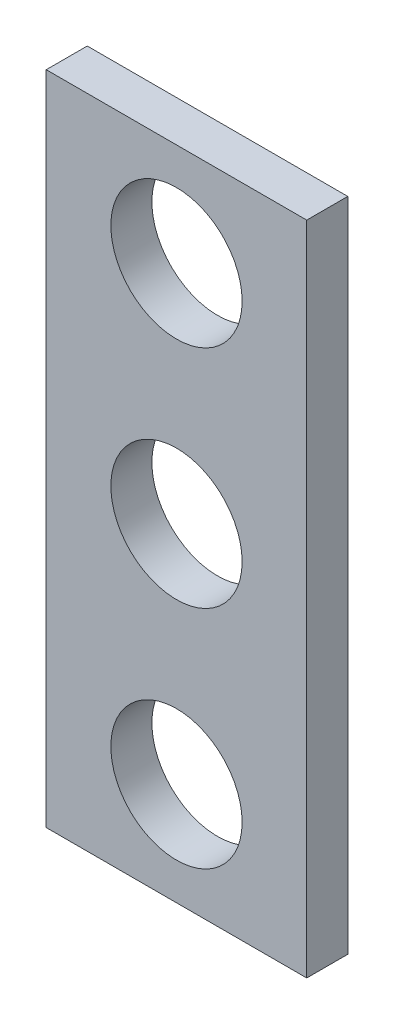
SolidWorks part; units mm, degrees
material "Plain Carbon Steel"
ref_plane "Front Plane" through (0, 0, 0) normal (0, 0, 1) x (1, 0, 0)
ref_plane "Top Plane" through (0, 0, 0) normal (0, 1, 0) x (1, 0, 0)
ref_plane "Right Plane" through (0, 0, 0) normal (1, 0, 0) x (0, 0, -1)
sketch "Sketch1" plane through (0, 0, 0) normal (0, 0, 1) x (1, 0, 0)
  line L0 (3.175, 177.7863) -> (3.175, 152.7863) construction
  line L1 (-3.175, 177.7863) -> (3.175, 177.7863)
  line L2 (-3.175, 177.7863) -> (-3.175, 161.7863)
  line L3 (-3.175, 161.7863) -> (3.175, 161.7863)
  line L4 (3.175, 177.7863) -> (3.175, 161.7863)
  line L5 (0, 169.7863) -> (3.175, 169.7863) construction
  circle A0 centre (0, 169.7863) radius 1.6
  circle A1 centre (0, 175.2863) radius 1.6
  circle A2 centre (0, 164.2863) radius 1.6
  dimension "D1" = 3.2
  dimension "D2" = 3.2
extrude "Boss-Extrude1" add sketch "Sketch1" along normal blind 1
